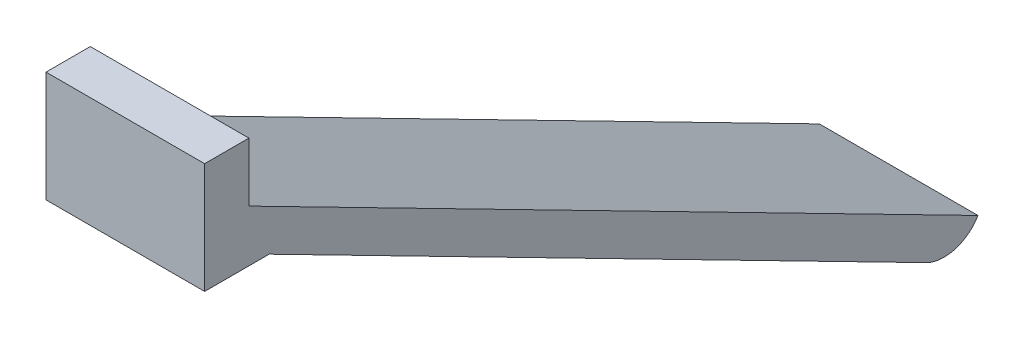
SolidWorks part; units mm, degrees
ref_plane "Front" through (0, 0, 0) normal (0, 0, 1) x (1, 0, 0)
ref_plane "Top" through (0, 0, 0) normal (0, 1, 0) x (1, 0, 0)
ref_plane "Right" through (0, 0, 0) normal (1, 0, 0) x (0, 0, -1)
sketch "Sketch1" plane through (0, 0, 0) normal (1, 0, 0) x (0, 0, -1)
  line L0 (-9.6761, -16.2117) -> (-29.4424, -6.1085)
  line L1 (-9.6761, -16.2117) -> (-9.6444, -16.1495)
  line L2 (-11.0839, -16.6152) -> (-28.8924, -7.5127)
  line L4 (-28.8924, -7.5127) -> (-30.6424, -7.5127)
  line L5 (-29.4424, -6.1085) -> (-29.4424, -4.5127)
  line L6 (-29.4424, -4.5127) -> (-30.6424, -4.5127)
  line L7 (-30.6424, -7.5127) -> (-30.6424, -4.5127)
  arc A0 (-9.6444, -16.1495) -> (-11.0839, -16.6152) centre (-10.597, -15.6626) cw
  dimension "D1" = 20
  dimension "D2" = 1.2
  dimension "D3" = 3
  dimension "D4" = 1
extrude "Boss-Extrude1" add sketch "Sketch1" along normal blind 4.3
